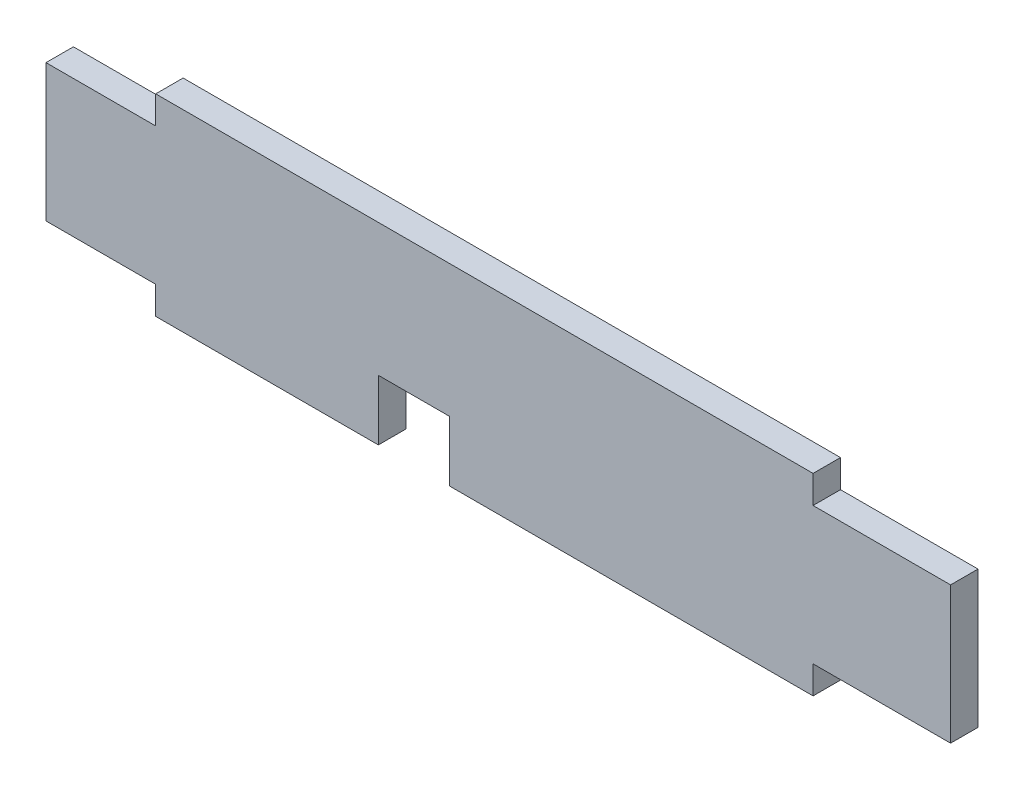
SolidWorks part; units mm, degrees
ref_plane "正面" through (0, 0, 0) normal (0, 0, 1) x (1, 0, 0)
ref_plane "平面" through (0, 0, 0) normal (0, 1, 0) x (1, 0, 0)
ref_plane "右側面" through (0, 0, 0) normal (1, 0, 0) x (0, 0, -1)
sketch "ｽｹｯﾁ1" plane through (0, 0, 0) normal (0, 0, 1) x (1, 0, 0)
  line L0 (164.93, 12.5) -> (177.1233, 12.5) construction
  line L1 (0, 0) -> (164.93, 0)
  line L2 (0, 0) -> (0, 25)
  line L3 (0, 25) -> (164.93, 25)
  line L4 (164.93, 0) -> (164.93, 25)
  line L5 (139.86, 25) -> (20, 25)
  line L6 (139.86, 25) -> (139.86, 30.07)
  line L7 (139.86, 30.07) -> (20, 30.07)
  line L8 (20, 25) -> (20, 30.07)
  line L9 (139.86, -5.07) -> (20, -5.07)
  line L10 (20, 0) -> (20, -5.07)
  line L11 (139.86, 0) -> (20, 0)
  line L12 (139.86, 0) -> (139.86, -5.07)
  line L13 (79.93, -5.07) -> (79.93, 14.4644) construction
  line L14 (73.6, -5.07) -> (60.6, -5.07)
  line L15 (73.6, -5.07) -> (73.6, 5.93)
  line L16 (73.6, 5.93) -> (60.6, 5.93)
  line L17 (60.6, -5.07) -> (60.6, 5.93)
  line L18 (67.1, 5.93) -> (67.1, -10.4919) construction
  point P9 (20, 27.535)
  dimension "D1" = 164.93
  dimension "D2" = 25
  dimension "D3" = 5.07
  dimension "D4" = 25.07
  dimension "D5" = 20
  dimension "D6" = 11
  dimension "D7" = 13
  dimension "D8" = 12.83
extrude "ﾎﾞｽ - 押し出し1" add sketch "ｽｹｯﾁ1" along normal blind 5 contours L1 L17 L16 L15 L11 L4 L3 L2 | L8 L3 L6 L7 | L9 L17 L1 L10 | L15 L9 L12 L11
